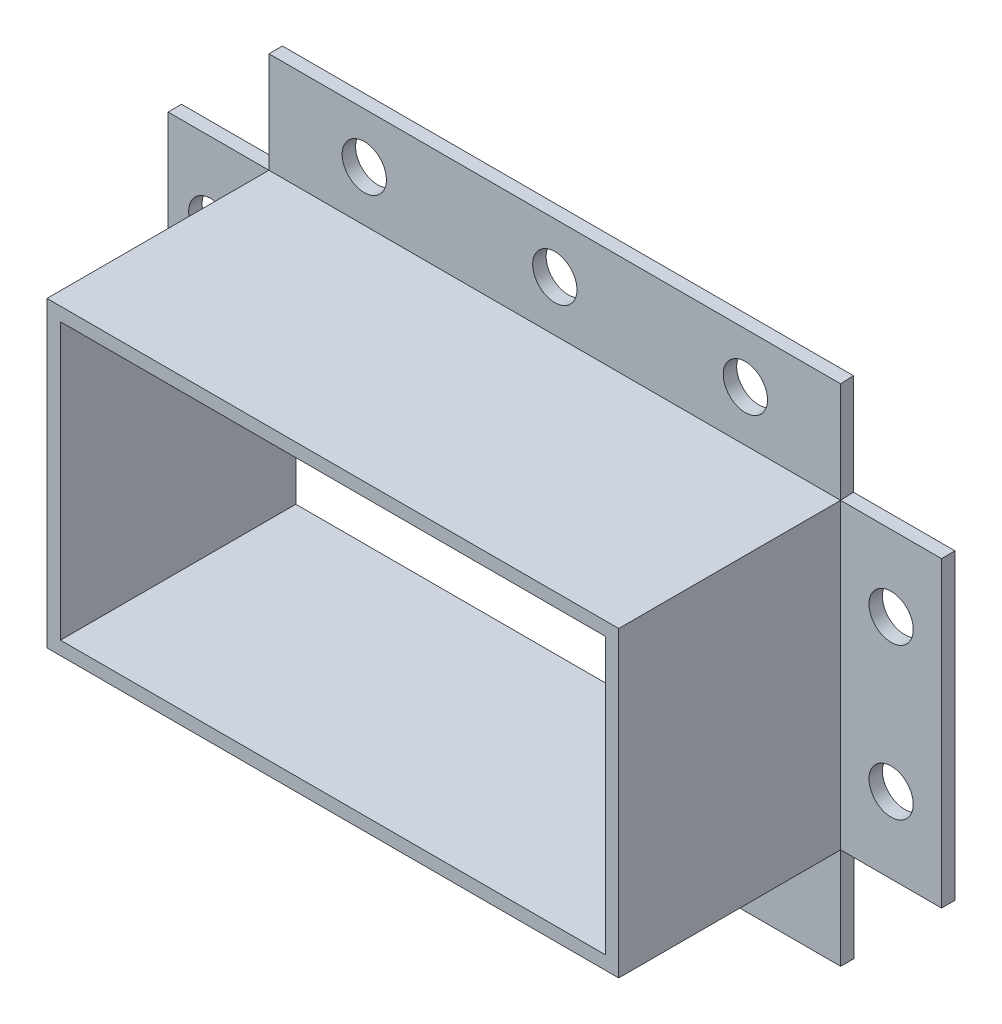
SolidWorks part; units mm, degrees
ref_plane "Plano frontal" through (0, 0, 0) normal (0, 0, 1) x (1, 0, 0)
ref_plane "Plano superior" through (0, 0, 0) normal (0, 1, 0) x (1, 0, 0)
ref_plane "Plano direito" through (0, 0, 0) normal (1, 0, 0) x (0, 0, -1)
sketch "Esboço1" plane through (0, 0, 0) normal (0, 0, 1) x (1, 0, 0)
  line L1 (-42.5, 22.5) -> (42.5, 22.5)
  line L2 (-42.5, 22.5) -> (-42.5, -22.5)
  line L3 (-42.5, -22.5) -> (42.5, -22.5)
  line L4 (42.5, 22.5) -> (42.5, -22.5)
  line L5 (-42.5, 22.5) -> (42.5, -22.5) construction
  line L6 (-42.5, -22.5) -> (42.5, 22.5) construction
  point P0 (0, 0)
  dimension "D1" = 85
  dimension "D2" = 45
extrude "Ressalto-extrusão1" add sketch "Esboço1" along normal blind 35
sketch "Esboço2" plane through (0, 0, 0) normal (0, 0, -1) x (-1, 0, 0)
  line L0 (-42.5, 22.5) -> (42.5, 22.5) construction
  line L1 (-40.5, 20.5) -> (40.5, 20.5)
  line L2 (-40.5, 20.5) -> (-40.5, -20.5)
  line L3 (-40.5, -20.5) -> (40.5, -20.5)
  line L4 (40.5, 20.5) -> (40.5, -20.5)
  line L5 (-40.5, 20.5) -> (40.5, -20.5) construction
  line L6 (-40.5, -20.5) -> (40.5, 20.5) construction
  line L7 (42.5, 22.5) -> (42.5, -22.5) construction
  point P0 (0, 0)
  dimension "D1" = 2
  dimension "D2" = 2
extrude "Corte-extrusão1" cut sketch "Esboço2" against normal blind 33
sketch "Esboço3" plane through (42.5, 0, 0) normal (1, 0, 0) x (0, 0, -1)
  line L0 (0, 22.5) -> (-2, 22.5)
  line L1 (-35, 22.5) -> (0, 22.5) construction
  line L2 (-2, 22.5) -> (-2, -22.5)
  line L3 (-35, -22.5) -> (0, -22.5) construction
  line L4 (-2, -22.5) -> (0, -22.5)
  line L5 (0, -22.5) -> (0, 22.5)
  dimension "D1" = 2
extrude "Ressalto-extrusão2" add sketch "Esboço3" along normal blind 15
sketch "Esboço4" plane through (0, 22.5, 0) normal (0, 1, 0) x (1, 0, 0)
  line L0 (42.3977, 0) -> (42.5, -2)
  line L1 (57.5, 0) -> (-42.5, 0) construction
  line L2 (42.3977, 0) -> (-42.5, 0)
  line L3 (-42.5, -2) -> (-42.5, 0)
  line L4 (-42.5, -35) -> (-42.5, 0) construction
  line L5 (42.5, -2) -> (-42.5, -2)
extrude "Ressalto-extrusão3" add sketch "Esboço4" along normal blind 15
sketch "Esboço5" plane through (-42.5, 0, 0) normal (-1, 0, 0) x (0, 0, 1)
  line L0 (2, 22.5) -> (0, 22.5)
  line L1 (0, 37.5) -> (0, -22.5) construction
  line L2 (0, 22.5) -> (0, -22.5)
  line L6 (2, 22.5) -> (2, -22.5)
  line L7 (35, -22.5) -> (0, -22.5) construction
  line L8 (2, -22.5) -> (0, -22.5)
extrude "Ressalto-extrusão4" add sketch "Esboço5" along normal blind 15
sketch "Esboço6" plane through (0, -22.5, 0) normal (0, -1, 0) x (1, 0, 0)
  line L0 (42.5, 2) -> (42.5, 0)
  line L1 (-57.5, 0) -> (57.5, 0) construction
  line L2 (-42.5, 2) -> (-42.5, 0)
  line L3 (-42.5, 0) -> (42.5, 0)
  line L4 (42.5, 2) -> (-42.5, 2)
extrude "Ressalto-extrusão5" add sketch "Esboço6" along normal blind 15
hole_wizard "Broca de rosquear de cano para tarraxa de 1/81" positions "Esboço7" profile "Esboço8" hole size "1/8" standard "Ansi Inch"
sketch "Esboço7" plane through (0, 0, 2) normal (0, 0, 1) x (1, 0, 0)
  line L0 (57.5, 22.5) -> (42.5, 22.5) construction
  line L4 (-42.5, 37.5) -> (-42.5, 22.5) construction
  line L7 (-42.5, -37.5) -> (-42.5, -22.5) construction
  line L9 (-57.5, -22.5) -> (-42.5, -22.5) construction
  line L13 (-42.5, 37.5) -> (42.5, 37.5) construction
  line L14 (42.5, -37.5) -> (-42.5, -37.5) construction
  line L15 (57.5, 22.5) -> (57.5, -22.5) construction
  point P0 (50, 11.25)
  point P2 (50, -11.25)
  point P4 (-51.1524, -11.25)
  point P6 (-51.1524, 11.25)
  point P8 (-28.33, 30)
  point P10 (0, 30)
  point P12 (28.33, 30)
  point P14 (28.33, -30)
  point P16 (0, -30)
  point P18 (-28.33, -30)
  point P29 (-42.5, 30)
  dimension "D1" = 22.5
  dimension "D2" = 11.25
  dimension "D3" = 14.17
  dimension "D4" = 28.33
  dimension "D5" = 28.33
  dimension "D6" = 14.17
  dimension "D7" = 28.33
  dimension "D8" = 28.33
  dimension "D9" = 22.5
  dimension "D10" = 11.25
  dimension "D11" = 7.5
  dimension "D12" = 7.5
  dimension "D13" = 7.5
  dimension "D14" = 7.5
  dimension "D15" = 7.5
  dimension "D16" = 7.5
  dimension "D17" = 7.5
sketch "Esboço8" plane through (50, 11.25, 2) normal (1, 0, 0) x (0, -1, 0)
  line L0 (0, 0) -> (0, 11.9768)
  line L1 (0, 11.9768) -> (3.29, 10)
  line L2 (3.29, 10) -> (3.29, 0)
  line L5 (3.29, 0) -> (0, 0)
  line L10 (0, 11.9768) -> (-3.29, 10) construction
  line L11 (0, -6.35) -> (0, 107.95) construction
  dimension "Hole Dia." = 6.58
  dimension "Hole Depth" = 10
  dimension "Drill Angle" = 118
sketch "Esboço9" plane through (0, 0, 35) normal (0, 0, 1) x (1, 0, 0)
  line L0 (42.5, -22.5) -> (42.5, 22.5) construction
  line L1 (40.5, 20.5) -> (-40.5, 20.5)
  line L2 (40.5, 20.5) -> (40.5, -20.5)
  line L3 (40.5, -20.5) -> (-40.5, -20.5)
  line L4 (-40.5, 20.5) -> (-40.5, -20.5)
  line L5 (40.5, 20.5) -> (-40.5, -20.5) construction
  line L6 (40.5, -20.5) -> (-40.5, 20.5) construction
  line L7 (-42.5, -22.5) -> (42.5, -22.5) construction
  point P0 (0, 0)
  dimension "D1" = 2
  dimension "D2" = 2
extrude "Corte-extrusão2" cut sketch "Esboço9" against normal up to next
